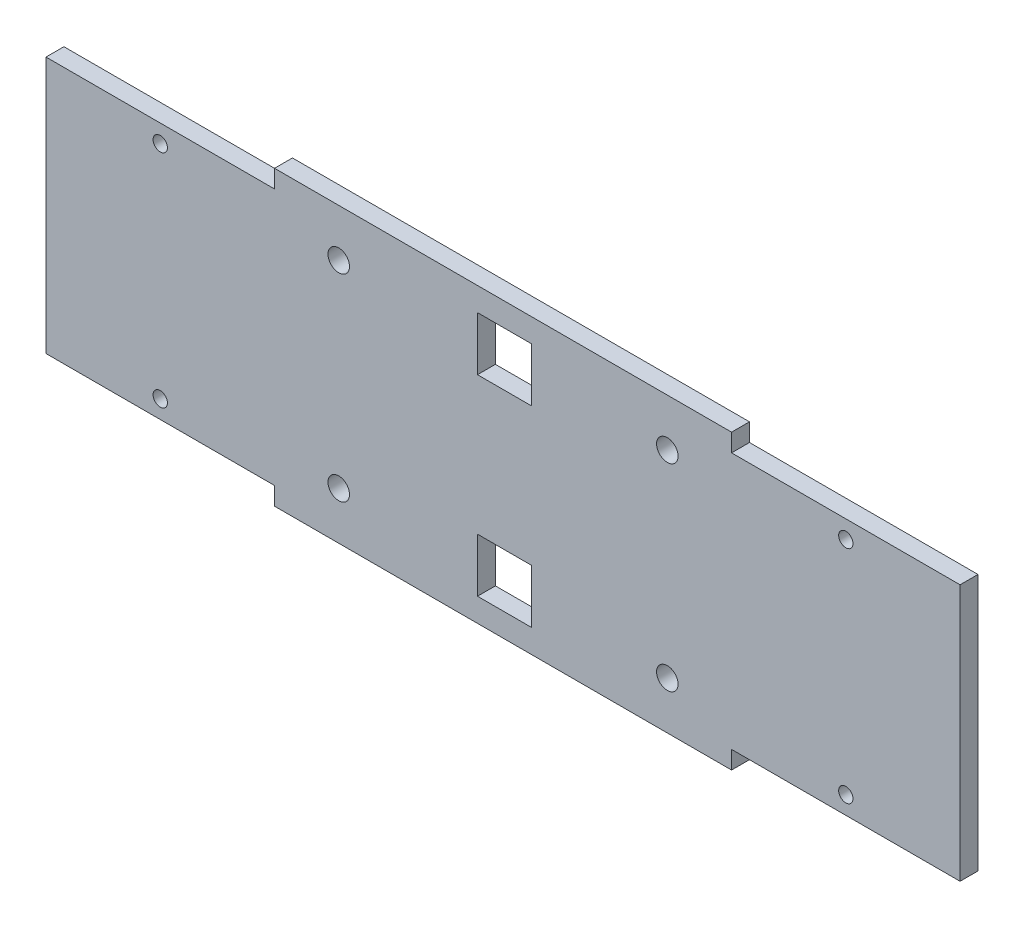
SolidWorks part; units mm, degrees
ref_plane "Front Plane" through (0, 0, 0) normal (0, 0, 1) x (1, 0, 0)
ref_plane "Top Plane" through (0, 0, 0) normal (0, 1, 0) x (1, 0, 0)
ref_plane "Right Plane" through (0, 0, 0) normal (1, 0, 0) x (0, 0, -1)
sketch "Sketch1" plane through (0, 0, 0) normal (0, 0, 1) x (1, 0, 0)
  line L0 (191.25, 71.6376) -> (255, 71.6376)
  line L1 (0, 0) -> (63.75, 0)
  line L2 (0, 0) -> (0, 71.6376)
  line L3 (0, 71.6376) -> (63.75, 71.6376)
  line L4 (255, 0) -> (255, 71.6376)
  line L5 (0, 71.6376) -> (63.75, 71.6376)
  line L6 (0, 71.6376) -> (0, 66.6376)
  line L9 (191.25, 76.6376) -> (191.25, 71.6376)
  line L11 (63.75, 71.6376) -> (63.75, 76.6376)
  line L12 (63.75, 76.6376) -> (127.5, 76.6376)
  line L14 (127.5, 76.6376) -> (191.25, 76.6376)
  line L16 (191.25, 71.6376) -> (255, 71.6376)
  line L18 (191.25, 0) -> (255, 0)
  line L19 (191.25, 0) -> (255, 0)
  line L20 (127.5, -5) -> (191.25, -5)
  line L21 (63.75, -5) -> (127.5, -5)
  line L22 (63.75, 0) -> (63.75, -5)
  line L23 (191.25, -5) -> (191.25, 0)
  line L24 (0, 0) -> (63.75, 0)
  line L25 (0, 0) -> (63.75, 0)
  line L26 (191.25, 0) -> (255, 0)
  line L27 (0, 35.8188) -> (9.0697, 35.8188)
  line L28 (135.3704, 55.0794) -> (120.3704, 55.0794)
  line L29 (135.3704, 55.0794) -> (135.3704, 70.0794)
  line L30 (135.3704, 70.0794) -> (120.3704, 70.0794)
  line L31 (120.3704, 55.0794) -> (120.3704, 70.0794)
  line L32 (120.3704, 16.5582) -> (120.3704, 1.5582)
  line L33 (135.3704, 1.5582) -> (120.3704, 1.5582)
  line L34 (135.3704, 16.5582) -> (135.3704, 1.5582)
  line L35 (127.5, -5) -> (191.25, -5)
  line L36 (63.75, -5) -> (127.5, -5)
  line L37 (135.3704, 16.5582) -> (120.3704, 16.5582)
  circle A0 centre (81.6684, 63.3585) radius 3
  circle A1 centre (173.3316, 63.3585) radius 3
  circle A2 centre (81.6684, 8.2791) radius 3
  circle A3 centre (173.3316, 8.2791) radius 3
  point P28 (173.3316, 35.8188)
extrude "Boss-Extrude1" add sketch "Sketch1" along normal blind 5 contours L20 L23 L18 L4 L0 L9 L14 L12 L11 L3 L2 L1 L22 L21 A3 A2 A1 A0
sketch "Sketch2" plane through (0, 0, 0) normal (0, 0, -1) x (-1, 0, 0)
  line L0 (-31.875, 0) -> (-31.875, 5)
  line L1 (0, 0) -> (-63.75, 0) construction
  line L2 (-31.875, 71.6376) -> (-31.875, 66.6376)
  line L3 (0, 71.6376) -> (-63.75, 71.6376) construction
  line L4 (-127.5, -5) -> (-127.5, 28.2662)
  line L5 (-63.75, -5) -> (-191.25, -5) construction
  circle A0 centre (-31.875, 5) radius 1.5
  circle A1 centre (-31.875, 66.6376) radius 1.5
  circle A2 centre (-223.125, 66.6376) radius 1.5
  circle A3 centre (-223.125, 5) radius 1.5
extrude "Cut-Extrude1" cut sketch "Sketch2" against normal blind 185
sketch "Sketch3" plane through (0, 0, 0) normal (0, 0, -1) x (-1, 0, 0)
  circle A0 centre (-31.875, 5) radius 2
  circle A1 centre (-31.875, 66.6376) radius 2
  circle A2 centre (-223.125, 5) radius 2
  circle A3 centre (-223.125, 66.6376) radius 2
extrude "Cut-Extrude2" cut sketch "Sketch3" against normal blind 10
